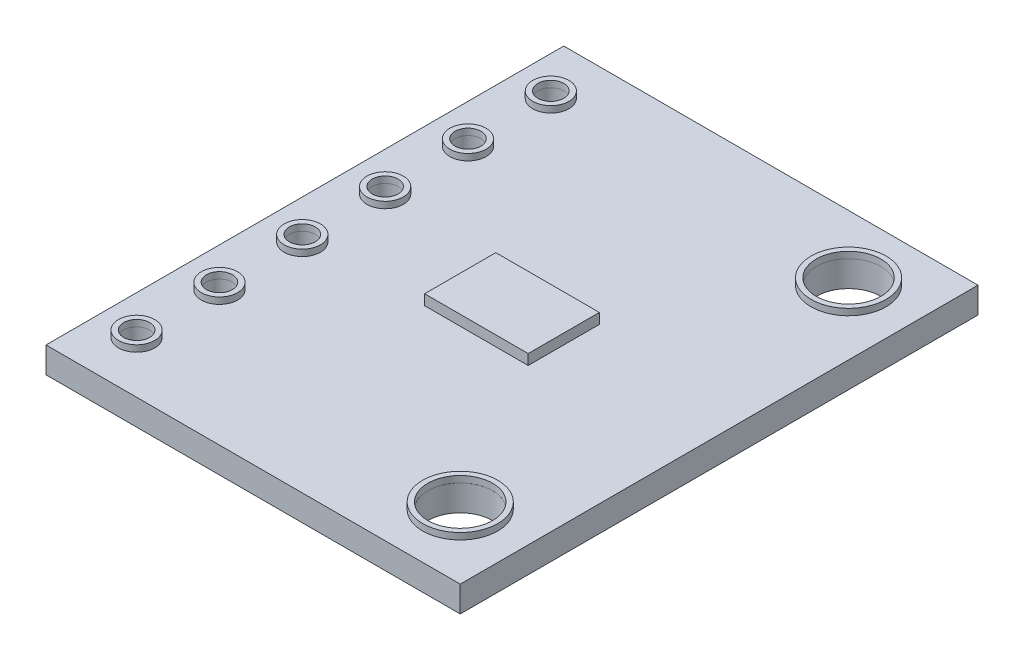
SolidWorks part; units mm, degrees
ref_plane "Front Plane" through (0, 0, 0) normal (0, 0, 1) x (1, 0, 0)
ref_plane "Top Plane" through (0, 0, 0) normal (0, 1, 0) x (1, 0, 0)
ref_plane "Right Plane" through (0, 0, 0) normal (1, 0, 0) x (0, 0, -1)
sketch "Sketch1" plane through (0, 0, 0) normal (0, 1, 0) x (1, 0, 0)
  line L1 (-8, -10) -> (8, -10)
  line L2 (-8, -10) -> (-8, 10)
  line L3 (-8, 10) -> (8, 10)
  line L4 (8, -10) -> (8, 10)
  line L5 (-8, -10) -> (8, 10) construction
  line L6 (-8, 10) -> (8, -10) construction
  point P0 (0, 0)
  dimension "D1" = 16
  dimension "D2" = 20
extrude "Boss-Extrude1" add sketch "Sketch1" along normal blind 1
sketch "Sketch2" plane through (0, 1, 0) normal (0, 1, 0) x (1, 0, 0)
  line L0 (-8, 10) -> (-8, -10) construction
  line L1 (8, 10) -> (-8, 10) construction
  line L2 (-6.5, 8) -> (-6.5, 4.8) construction
  line L3 (8, -10) -> (8, 10) construction
  line L4 (-8, 0) -> (8, 0) construction
  circle A0 centre (-6.5, 8) radius 0.5
  circle A1 centre (-6.5, 4.8) radius 0.5
  circle A2 centre (-6.5, 1.6) radius 0.5
  circle A3 centre (-6.5, -1.6) radius 0.5
  circle A4 centre (-6.5, -4.8) radius 0.5
  circle A5 centre (-6.5, -8) radius 0.5
  circle A6 centre (5.5, 7.5) radius 1.25
  circle A7 centre (5.5, -7.5) radius 1.25
  dimension "D1" = 1
  dimension "D6" = 2.5
  dimension "D2" = 1.5
  dimension "D3" = 2
  dimension "D5" = 3.2
  dimension "D7" = 2.5
  dimension "D8" = 2.5
  dimension "D4" = 6
extrude "Cut-Extrude1" cut sketch "Sketch2" against normal blind 1
sketch "Sketch3" plane through (0, 1, 0) normal (0, 1, 0) x (1, 0, 0)
  circle A0 centre (5.5, -7.5) radius 1.25 construction
  circle A1 centre (5.5, 7.5) radius 1.25 construction
  circle A2 centre (-6.5, -8) radius 0.5 construction
  circle A3 centre (-6.5, -4.8) radius 0.5 construction
  circle A4 centre (-6.5, -1.6) radius 0.5 construction
  circle A5 centre (-6.5, 1.6) radius 0.5 construction
  circle A6 centre (-6.5, 4.8) radius 0.5 construction
  circle A7 centre (-6.5, 8) radius 0.5 construction
  circle A8 centre (5.5, -7.5) radius 1.25
  circle A9 centre (5.5, 7.5) radius 1.25
  circle A10 centre (-6.5, -8) radius 0.5
  circle A11 centre (-6.5, -4.8) radius 0.5
  circle A12 centre (-6.5, -1.6) radius 0.5
  circle A13 centre (-6.5, 1.6) radius 0.5
  circle A14 centre (-6.5, 4.8) radius 0.5
  circle A15 centre (-6.5, 8) radius 0.5
  circle A16 centre (5.5, -7.5) radius 1.45
  circle A17 centre (5.5, 7.5) radius 1.45
  circle A18 centre (-6.5, -8) radius 0.7
  circle A19 centre (-6.5, -4.8) radius 0.7
  circle A20 centre (-6.5, -1.6) radius 0.7
  circle A21 centre (-6.5, 1.6) radius 0.7
  circle A22 centre (-6.5, 4.8) radius 0.7
  circle A23 centre (-6.5, 8) radius 0.7
  dimension "D1" = 0.2
extrude "Boss-Extrude2" add sketch "Sketch3" along normal blind 0.25 separate body
sketch "Sketch4" plane through (0, 1, 0) normal (0, 1, 0) x (1, 0, 0)
  line L1 (-2, -1.375) -> (2, -1.375)
  line L2 (-2, -1.375) -> (-2, 1.375)
  line L3 (-2, 1.375) -> (2, 1.375)
  line L4 (2, -1.375) -> (2, 1.375)
  line L5 (-2, -1.375) -> (2, 1.375) construction
  line L6 (-2, 1.375) -> (2, -1.375) construction
  point P0 (0, 0)
  dimension "D1" = 2.75
  dimension "D2" = 4
extrude "Boss-Extrude3" add sketch "Sketch4" along normal blind 0.4 separate body
